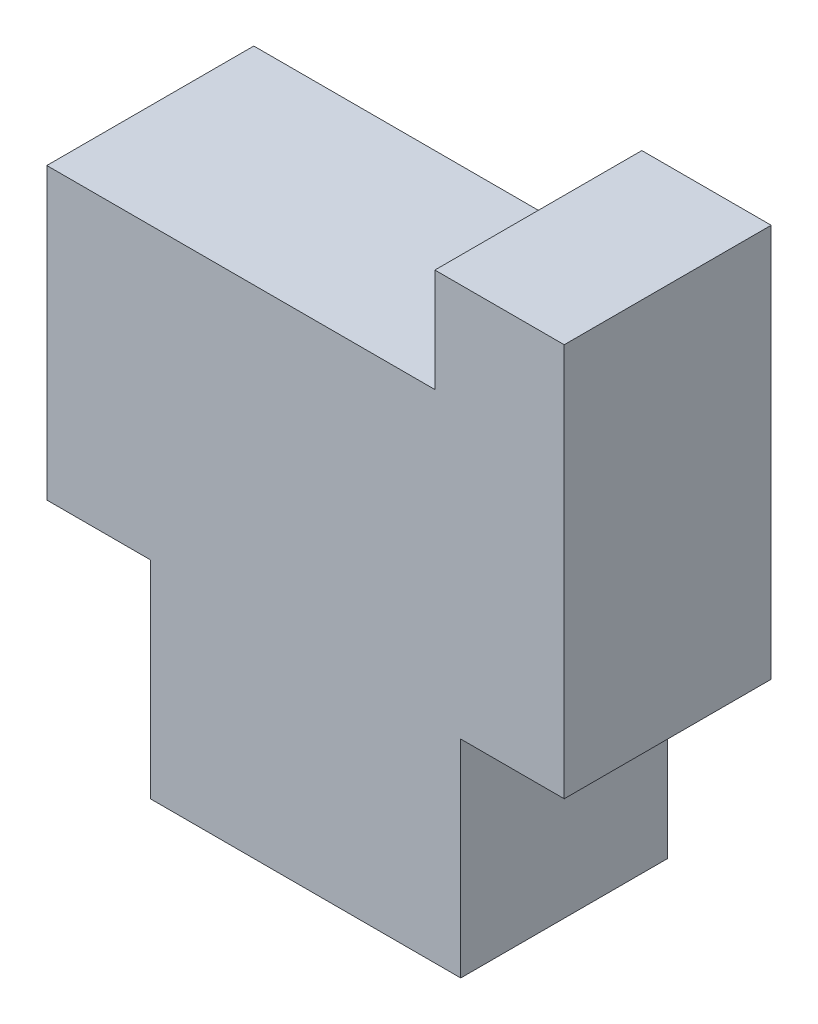
SolidWorks part; units mm, degrees
ref_plane "Front Plane" through (0, 0, 0) normal (0, 0, 1) x (1, 0, 0)
ref_plane "Top Plane" through (0, 0, 0) normal (0, 1, 0) x (1, 0, 0)
ref_plane "Right Plane" through (0, 0, 0) normal (1, 0, 0) x (0, 0, -1)
sketch "Sketch1" plane through (0, 0, 0) normal (0, 0, 1) x (1, 0, 0)
  line L0 (0, 0) -> (6, 0)
  line L1 (0, 0) -> (0, 4)
  line L2 (6, 0) -> (6, 4)
  line L3 (6, 4) -> (8, 4)
  line L4 (-2, 9.6) -> (5.5, 9.6)
  line L5 (5.5, 9.6) -> (5.5, 11.6)
  line L6 (5.5, 11.6) -> (8, 11.6)
  line L7 (8, 11.6) -> (8, 4)
  line L8 (0, 4) -> (-2, 4)
  line L9 (-2, 4) -> (-2, 9.6)
  dimension "D1" = 6
  dimension "D2" = 8
  dimension "D3" = 7.6
  dimension "D4" = 2.5
  dimension "D5" = 9.6
extrude "Boss-Extrude1" add sketch "Sketch1" along normal blind 4
